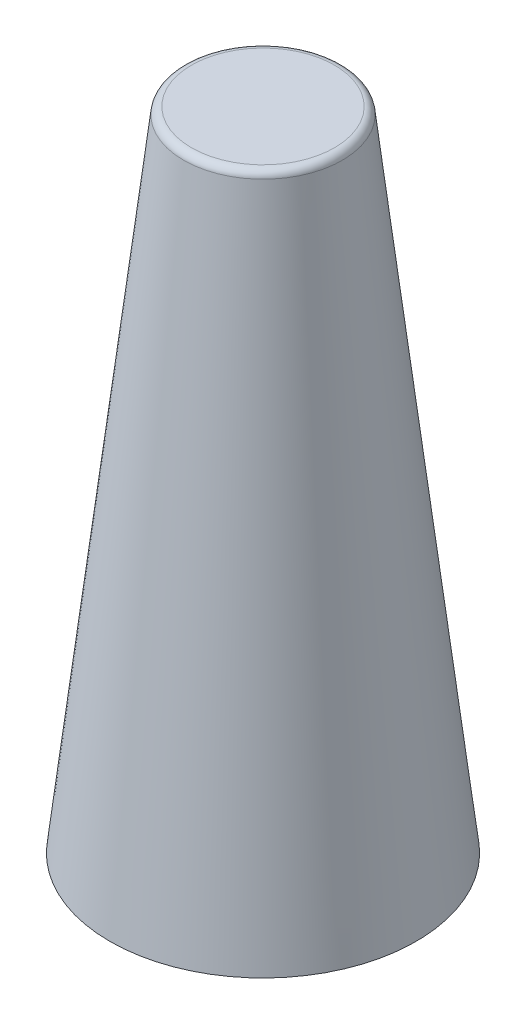
SolidWorks part; units mm, degrees
ref_plane "Front Plane" through (0, 0, 0) normal (0, 0, 1) x (1, 0, 0)
ref_plane "Top Plane" through (0, 0, 0) normal (0, 1, 0) x (1, 0, 0)
ref_plane "Right Plane" through (0, 0, 0) normal (1, 0, 0) x (0, 0, -1)
sketch "Sketch1" plane through (0, 0, 0) normal (0, 0, 1) x (1, 0, 0)
  line L0 (0, 416.6696) -> (0, -406.3304) construction
  line L1 (0, 416.6696) -> (-100, 416.6696)
  line L2 (0, -406.3304) -> (-195, -406.3304)
  line L3 (-100, 416.6696) -> (-195, -406.3304)
  line L4 (0, 406.6696) -> (-96.1211, 406.6696)
  line L5 (0, -396.3304) -> (-188.8125, -396.3304)
  line L6 (-96.1211, 406.6696) -> (-188.8125, -396.3304)
  point P9 (-837.1179, -80.5763)
  dimension "D1" = 823
  dimension "D2" = 10
  dimension "D3" = 5
  dimension "D4" = 10
  dimension "D5" = 5
revolve "Revolve1" add sketch "Sketch1" angle 360 about L0
fillet "Fillet1" radius 10 1 edges at (0, 416.6696, 100)
